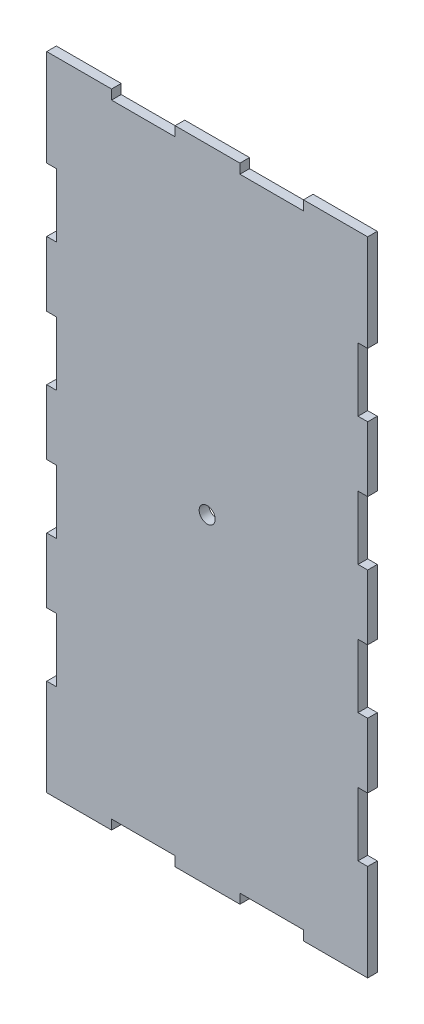
SolidWorks part; units mm, degrees
ref_plane "Front Plane" through (0, 0, 0) normal (0, 0, 1) x (1, 0, 0)
ref_plane "Top Plane" through (0, 0, 0) normal (0, 1, 0) x (1, 0, 0)
ref_plane "Right Plane" through (0, 0, 0) normal (1, 0, 0) x (0, 0, -1)
sketch "Sketch1" plane through (0, 0, 0) normal (0, 0, 1) x (1, 0, 0)
  line L0 (60.2, 200) -> (60.2, 197)
  line L1 (0, 0) -> (100, 0)
  line L2 (0, 0) -> (0, 200)
  line L3 (0, 200) -> (100, 200)
  line L4 (100, 0) -> (100, 200)
  line L5 (20.2, 200) -> (40, 200)
  line L6 (20.2, 200) -> (20.2, 197)
  line L7 (20.2, 197) -> (40, 197)
  line L8 (40, 200) -> (40, 197)
  line L9 (60.2, 200) -> (80, 200)
  line L10 (80, 200) -> (80, 197)
  line L11 (60.2, 197) -> (80, 197)
  line L12 (0, 129.9) -> (0, 110.1)
  line L13 (0, 169.9) -> (3, 169.9)
  line L14 (0, 169.9) -> (0, 150.1)
  line L15 (0, 150.1) -> (3, 150.1)
  line L16 (3, 169.9) -> (3, 150.1)
  line L17 (0, 129.9) -> (3, 129.9)
  line L18 (3, 129.9) -> (3, 110.1)
  line L19 (0, 110.1) -> (3, 110.1)
  line L20 (0, 89.9) -> (0, 70.1)
  line L21 (0, 89.9) -> (3, 89.9)
  line L22 (3, 89.9) -> (3, 70.1)
  line L23 (0, 70.1) -> (3, 70.1)
  line L24 (0, 49.9) -> (0, 30.1)
  line L25 (0, 49.9) -> (3, 49.9)
  line L26 (3, 49.9) -> (3, 30.1)
  line L27 (0, 30.1) -> (3, 30.1)
  line L28 (-900, 100) -> (49100, 100) construction
  line L29 (50, -800) -> (50, 49200) construction
  line L30 (20.2, 3) -> (40, 3)
  line L31 (40, 0) -> (40, 3)
  line L32 (20.2, 0) -> (40, 0)
  line L33 (20.2, 0) -> (20.2, 3)
  line L34 (60.2, 0) -> (80, 0)
  line L35 (80, 0) -> (80, 3)
  line L36 (60.2, 3) -> (80, 3)
  line L37 (60.2, 0) -> (60.2, 3)
  line L38 (100, 49.9) -> (97, 49.9)
  line L39 (97, 49.9) -> (97, 30.1)
  line L40 (100, 30.1) -> (97, 30.1)
  line L41 (100, 49.9) -> (100, 30.1)
  line L42 (100, 89.9) -> (97, 89.9)
  line L43 (97, 89.9) -> (97, 70.1)
  line L44 (100, 70.1) -> (97, 70.1)
  line L45 (100, 89.9) -> (100, 70.1)
  line L46 (100, 129.9) -> (97, 129.9)
  line L47 (97, 129.9) -> (97, 110.1)
  line L48 (100, 110.1) -> (97, 110.1)
  line L49 (100, 129.9) -> (100, 110.1)
  line L50 (100, 150.1) -> (97, 150.1)
  line L51 (97, 169.9) -> (97, 150.1)
  line L52 (100, 169.9) -> (97, 169.9)
  line L53 (100, 169.9) -> (100, 150.1)
  circle A0 centre (50, 100) radius 2.5
  point P32 (100, 100)
  point P35 (50, 200)
  point P60 (50, 100)
  dimension "D13" = 5
  dimension "D1" = 200
  dimension "D2" = 100
  dimension "D3" = 20.2
  dimension "D4" = 19.8
  dimension "D5" = 3
  dimension "D7" = 20.2
  dimension "D8" = 30.1
  dimension "D9" = 19.8
  dimension "D10" = 3
  dimension "D12" = 20.2
  dimension "D6" = 2
  dimension "D11" = 4
extrude "Boss-Extrude1" add sketch "Sketch1" along normal blind 3 contours L52 L4 L3 L10 L11 L0 L8 L7 L6 L2 L13 L16 L15 L17 L18 L19 L21 L22 L23 L25 L26 L27 L1 L33 L30 L31 L37 L36 L35 L40 L39 L38 L44 L43 L42 L48 L47 L46 L50
